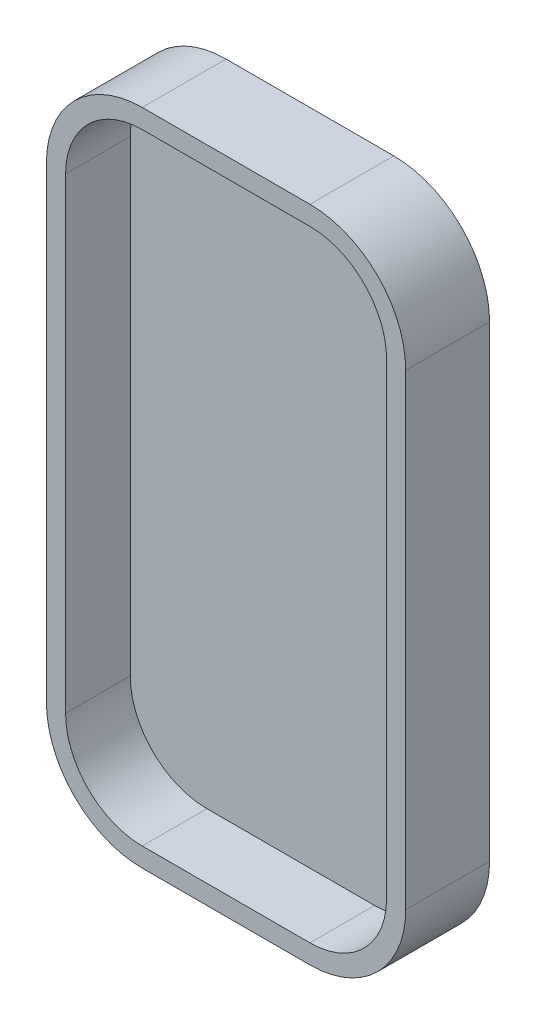
SolidWorks part; units mm, degrees
material "ABS"
ref_plane "Front Plane" through (0, 0, 0) normal (1, 0, 0) x (0, 1, 0)
ref_plane "Top Plane" through (0, 0, 0) normal (0, 0, 1) x (0, 1, 0)
ref_plane "Right Plane" through (0, 0, 0) normal (0, 1, 0) x (-1, 0, 0)
sketch "Sketch1" plane through (0, 0, 0) normal (0, 0, 1) x (0, 1, 0)
  line L1 (-19.5, 15) -> (19.5, 15)
  line L2 (-27.5, 7) -> (-27.5, -7)
  line L3 (-19.5, -15) -> (19.5, -15)
  line L4 (27.5, 7) -> (27.5, -7)
  line L5 (-27.5, 15) -> (27.5, -15) construction
  line L6 (-27.5, -15) -> (27.5, 15) construction
  arc A0 (-19.5, 15) -> (-27.5, 7) centre (-19.5, 7) ccw
  arc A1 (-27.5, -7) -> (-19.5, -15) centre (-19.5, -7) ccw
  arc A2 (19.5, -15) -> (27.5, -7) centre (19.5, -7) ccw
  arc A3 (19.5, 15) -> (27.5, 7) centre (19.5, 7) cw
  point P0 (0, 0)
  dimension "D3" = 8
  dimension "D1" = 55
  dimension "D2" = 30
extrude "Boss-Extrude1" add sketch "Sketch1" along normal blind 7
sketch "Sketch2" plane through (0, 0, 7) normal (0, 0, 1) x (1, 0, 0)
  line L1 (7, -25.9) -> (-7, -25.9)
  line L2 (13.4, -19.5) -> (13.4, 19.5)
  line L3 (7, 25.9) -> (-7, 25.9)
  line L4 (-13.4, -19.5) -> (-13.4, 19.5)
  line L5 (13.4, -25.9) -> (-13.4, 25.9) construction
  line L6 (13.4, 25.9) -> (-13.4, -25.9) construction
  line L8 (7, 27.5) -> (-7, 27.5) construction
  line L9 (15, -19.5) -> (15, 19.5) construction
  arc A0 (7, -25.9) -> (13.4, -19.5) centre (7, -19.5) ccw
  arc A1 (-7, -25.9) -> (-13.4, -19.5) centre (-7, -19.5) cw
  arc A2 (13.4, 19.5) -> (7, 25.9) centre (7, 19.5) ccw
  arc A3 (-7, 25.9) -> (-13.4, 19.5) centre (-7, 19.5) ccw
  point P0 (0, 0)
  point P8 (0, 27.5)
  dimension "D3" = 6.4
  dimension "D1" = 1.6
  dimension "D2" = 1.6
extrude "Cut-Extrude1" cut sketch "Sketch2" against normal blind 5.4
